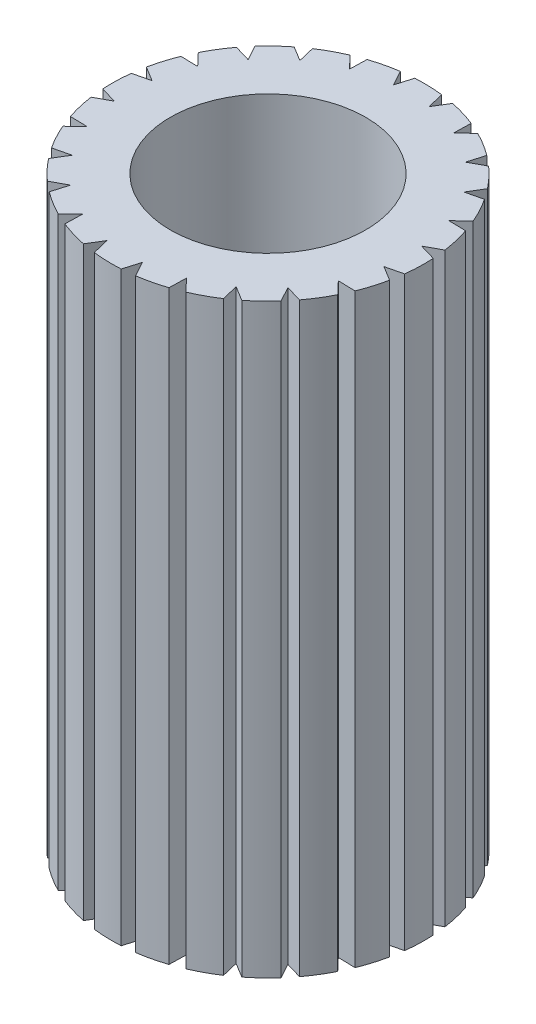
SolidWorks part; units mm, degrees
ref_plane "前视基准面" through (0, 0, 0) normal (0, 0, 1) x (1, 0, 0)
ref_plane "上视基准面" through (0, 0, 0) normal (0, 1, 0) x (1, 0, 0)
ref_plane "右视基准面" through (0, 0, 0) normal (1, 0, 0) x (0, 0, -1)
sketch "草图1" plane through (0, 0, 0) normal (0, 1, 0) x (1, 0, 0)
  line L0 (-0.2281, 1.5837) -> (-0.144, 1.4291)
  line L1 (-0.144, 1.4291) -> (-0.0944, 1.5972)
  line L2 (0.2308, 1.4177) -> (0.3222, 1.5672)
  line L3 (0.1895, 1.5887) -> (0.2308, 1.4177)
  line L4 (0.5898, 1.3097) -> (0.7168, 1.4304)
  line L5 (0.5943, 1.4855) -> (0.5898, 1.3097)
  line L6 (0.9087, 1.1124) -> (1.0626, 1.1962)
  line L7 (0.9585, 1.2811) -> (0.9087, 1.1124)
  line L8 (1.1657, 0.8393) -> (1.336, 0.8804)
  line L9 (1.2574, 0.9894) -> (1.1657, 0.8393)
  line L10 (1.3432, 0.509) -> (1.5183, 0.5046)
  line L11 (1.4707, 0.6302) -> (1.3432, 0.509)
  line L12 (1.4291, 0.144) -> (1.5972, 0.0944)
  line L13 (1.5837, 0.2281) -> (1.4291, 0.144)
  line L14 (1.4177, -0.2308) -> (1.5672, -0.3222)
  line L15 (1.5887, -0.1895) -> (1.4177, -0.2308)
  line L16 (1.3097, -0.5898) -> (1.4304, -0.7168)
  line L17 (1.4855, -0.5943) -> (1.3097, -0.5898)
  line L18 (1.1124, -0.9087) -> (1.1962, -1.0626)
  line L19 (1.2811, -0.9585) -> (1.1124, -0.9087)
  line L20 (0.8393, -1.1657) -> (0.8804, -1.336)
  line L21 (0.9894, -1.2574) -> (0.8393, -1.1657)
  line L22 (0.509, -1.3432) -> (0.5046, -1.5183)
  line L23 (0.6302, -1.4707) -> (0.509, -1.3432)
  line L24 (0.144, -1.4291) -> (0.0944, -1.5972)
  line L25 (0.2281, -1.5837) -> (0.144, -1.4291)
  line L26 (-0.2308, -1.4177) -> (-0.3222, -1.5672)
  line L27 (-0.1895, -1.5887) -> (-0.2308, -1.4177)
  line L28 (-0.5898, -1.3097) -> (-0.7168, -1.4304)
  line L29 (-0.5943, -1.4855) -> (-0.5898, -1.3097)
  line L30 (-0.9087, -1.1124) -> (-1.0626, -1.1962)
  line L31 (-0.9585, -1.2811) -> (-0.9087, -1.1124)
  line L32 (-1.1657, -0.8393) -> (-1.336, -0.8804)
  line L33 (-1.2574, -0.9894) -> (-1.1657, -0.8393)
  line L34 (-1.3432, -0.509) -> (-1.5183, -0.5046)
  line L35 (-1.4707, -0.6302) -> (-1.3432, -0.509)
  line L36 (-1.4291, -0.144) -> (-1.5972, -0.0944)
  line L37 (-1.5837, -0.2281) -> (-1.4291, -0.144)
  line L38 (-1.4177, 0.2308) -> (-1.5672, 0.3222)
  line L39 (-1.5887, 0.1895) -> (-1.4177, 0.2308)
  line L40 (-1.3097, 0.5898) -> (-1.4304, 0.7168)
  line L41 (-1.4855, 0.5943) -> (-1.3097, 0.5898)
  line L42 (-1.1124, 0.9087) -> (-1.1962, 1.0626)
  line L43 (-1.2811, 0.9585) -> (-1.1124, 0.9087)
  line L44 (-0.8393, 1.1657) -> (-0.8804, 1.336)
  line L45 (-0.9894, 1.2574) -> (-0.8393, 1.1657)
  line L46 (-0.509, 1.3432) -> (-0.5046, 1.5183)
  line L47 (-0.6302, 1.4707) -> (-0.509, 1.3432)
  arc A0 (-1.2811, 0.9585) -> (-1.4304, 0.7168) centre (0, 0) ccw
  circle A1 centre (0, 0) radius 1
  arc A2 (-0.9894, 1.2574) -> (-1.1962, 1.0626) centre (0, 0) ccw
  arc A3 (-0.6302, 1.4707) -> (-0.8804, 1.336) centre (0, 0) ccw
  arc A4 (-0.2281, 1.5837) -> (-0.5046, 1.5183) centre (0, 0) ccw
  arc A5 (0.1895, 1.5887) -> (-0.0944, 1.5972) centre (0, 0) ccw
  arc A6 (0.5943, 1.4855) -> (0.3222, 1.5672) centre (0, 0) ccw
  arc A7 (0.9585, 1.2811) -> (0.7168, 1.4304) centre (0, 0) ccw
  arc A8 (1.2574, 0.9894) -> (1.0626, 1.1962) centre (0, 0) ccw
  arc A9 (1.4707, 0.6302) -> (1.336, 0.8804) centre (0, 0) ccw
  arc A10 (1.5837, 0.2281) -> (1.5183, 0.5046) centre (0, 0) ccw
  arc A11 (1.5887, -0.1895) -> (1.5972, 0.0944) centre (0, 0) ccw
  arc A12 (1.4855, -0.5943) -> (1.5672, -0.3222) centre (0, 0) ccw
  arc A13 (1.2811, -0.9585) -> (1.4304, -0.7168) centre (0, 0) ccw
  arc A14 (0.9894, -1.2574) -> (1.1962, -1.0626) centre (0, 0) ccw
  arc A15 (0.6302, -1.4707) -> (0.8804, -1.336) centre (0, 0) ccw
  arc A16 (0.2281, -1.5837) -> (0.5046, -1.5183) centre (0, 0) ccw
  arc A17 (-0.1895, -1.5887) -> (0.0944, -1.5972) centre (0, 0) ccw
  arc A18 (-0.5943, -1.4855) -> (-0.3222, -1.5672) centre (0, 0) ccw
  arc A19 (-0.9585, -1.2811) -> (-0.7168, -1.4304) centre (0, 0) ccw
  arc A20 (-1.2574, -0.9894) -> (-1.0626, -1.1962) centre (0, 0) ccw
  arc A21 (-1.4707, -0.6302) -> (-1.336, -0.8804) centre (0, 0) ccw
  arc A22 (-1.5837, -0.2281) -> (-1.5183, -0.5046) centre (0, 0) ccw
  arc A23 (-1.5887, 0.1895) -> (-1.5972, -0.0944) centre (0, 0) ccw
  arc A24 (-1.4855, 0.5943) -> (-1.5672, 0.3222) centre (0, 0) ccw
  point P79 (0, 0)
  dimension "D1" = 3.2
  dimension "D2" = 2
  dimension "D3" = 45
  dimension "D4" = 24
extrude "凸台-拉伸1" add sketch "草图1" along normal blind 6
